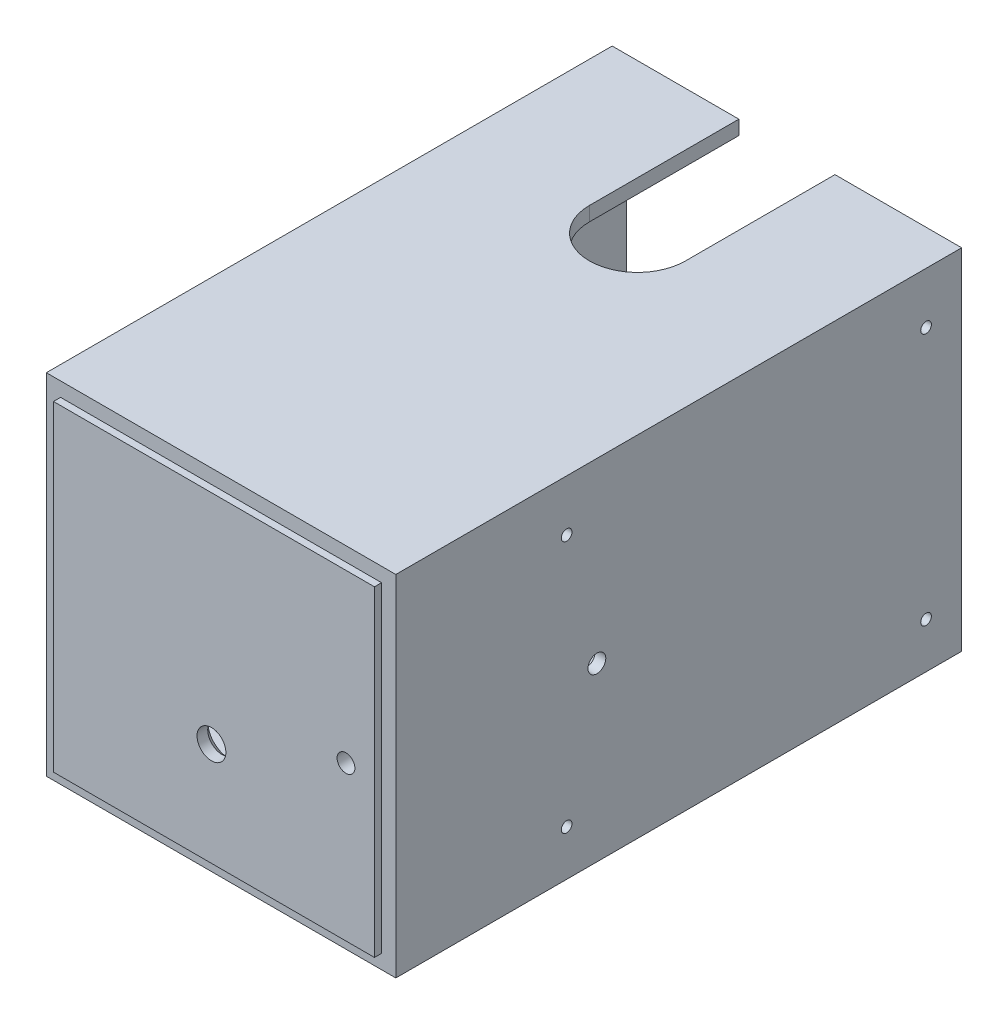
SolidWorks part; units mm, degrees
ref_plane "Alzado" through (0, 0, 0) normal (0, 0, 1) x (1, 0, 0)
ref_plane "Planta" through (0, 0, 0) normal (0, 1, 0) x (1, 0, 0)
ref_plane "Vista lateral" through (0, 0, 0) normal (1, 0, 0) x (0, 0, -1)
sketch "Croquis1" plane through (0, 0, 0) normal (0, 0, 1) x (1, 0, 0)
  line L1 (-49.1, 49.1) -> (49.1, 49.1)
  line L2 (-49.1, 49.1) -> (-49.1, -49.1)
  line L3 (-49.1, -49.1) -> (49.1, -49.1)
  line L4 (49.1, 49.1) -> (49.1, -49.1)
  point P4 (0, 49.1)
  point P6 (49.1, 0)
  dimension "D1" = 98.2
  dimension "D2" = 98.2
extrude "Saliente-Extruir1" add sketch "Croquis1" along normal blind 160.5 and the other way blind 0.5
sketch "Croquis4" plane through (0, -49.1, 0) normal (0, -1, 0) x (1, 0, 0)
  line L0 (-49.1, -0.5) -> (49.1, -0.5) construction
  line L1 (-13.5, 41.5) -> (-13.5, -0.5)
  line L2 (-13.5, -0.5) -> (13.5, -0.5)
  line L3 (13.5, -0.5) -> (13.5, 41.5)
  arc A0 (13.5, 41.5) -> (-13.5, 41.5) centre (0, 41.5) ccw
  dimension "D1" = 27
  dimension "D2" = 42
sketch "Croquis7" plane through (0, 0, -0.5) normal (0, 0, -1) x (-1, 0, 0)
  line L1 (-46.0987, 45.1) -> (45.0697, 45.1)
  line L2 (-46.0987, 45.1) -> (-46.0987, -45.1)
  line L3 (-46.0987, -45.1) -> (45.0697, -45.1)
  line L4 (45.0697, 45.1) -> (45.0697, -45.1)
  point P4 (45.0697, 0)
  dimension "D1" = 90.2
extrude "Cortar-Extruir3" cut sketch "Croquis7" against normal blind 156
extrude "puertas_laterales" cut sketch "Croquis4" against normal through all
sketch "Croquis10" plane through (0, 0, 160.5) normal (0, 0, 1) x (1, 0, 0)
  line L0 (-49.1, 49.1) -> (-49.1, -49.1) construction
  line L1 (-45.1, 45.1) -> (45.1, 45.1)
  line L2 (-45.1, 45.1) -> (-45.1, -45.1)
  line L3 (-45.1, -45.1) -> (45.1, -45.1)
  line L4 (45.1, 45.1) -> (45.1, -45.1)
  line L5 (49.1, 49.1) -> (-49.1, 49.1) construction
  line L6 (49.1, -49.1) -> (49.1, 49.1) construction
  line L7 (-49.1, -49.1) -> (49.1, -49.1) construction
  dimension "D1" = 4
  dimension "D2" = 4
  dimension "D3" = 4
  dimension "D4" = 4
extrude "parte_sup" cut sketch "Croquis10" against normal blind 2 flip side to cut
fillet "Redondeo1" radius 2 4 edges at (-45.0697, -45.1, 77.5) (-45.0697, 45.1, 77.5) (46.0987, -45.1, 77.5) (46.0987, 45.1, 77.5)
sketch "Croquis13" plane through (0, 0, 160.5) normal (0, 0, 1) x (1, 0, 0)
  line L1 (-45.1, 45.1) -> (45.1, 45.1)
  line L2 (-45.1, 45.1) -> (-45.1, -45.1)
  line L3 (-45.1, -45.1) -> (45.1, -45.1)
  line L4 (45.1, 45.1) -> (45.1, -45.1)
  line L5 (-13, -6.1) -> (13, -6.1)
  line L6 (-13, -6.1) -> (-13, -45.1)
  line L7 (-13, -45.1) -> (13, -45.1)
  line L8 (13, -6.1) -> (13, -45.1)
  line L9 (-7.5, -45.1) -> (7.2959, -45.1)
  line L10 (-7.5, -45.1) -> (-7.5, -28.18)
  line L12 (7.2959, -45.1) -> (7.2959, -30.646)
  circle A0 centre (-0.7041, -16.1) radius 4.05
  point P10 (0, -45.1)
  point P11 (0, -6.1)
  dimension "D7" = 8.1
  dimension "D8" = 44.3959
  dimension "D1" = 26
  dimension "D2" = 39
  dimension "D3" = 15
  dimension "D4" = 16.92
  dimension "D5" = 8
  dimension "D6" = 29
extrude "Cortar-Extruir7" cut sketch "Croquis13" against normal blind 6 contours A0
sketch "altura_piso_a_numeros" plane through (0, 49.1, 0) normal (0, 1, 0) x (1, 0, 0)
  line L5 (-72.9645, -59.0082) -> (89.6, -59.0082) construction
  line L6 (73.8227, -140.9384) -> (71.8227, -140.9384) construction
  dimension "D1" = 81.9302
sketch "altura_num_cam" plane through (0, 49.1, 0) normal (0, 1, 0) x (1, 0, 0)
  line L0 (48.8905, -59.0082) -> (49.1, -149.0082) construction
  line L1 (-72.9645, -59.0082) -> (89.6, -59.0082) construction
  line L2 (49.1, -158.5) -> (49.1, 0.5) construction
  dimension "D1" = 90
sketch "sim_ancho_cam" plane through (0, -49.1, 0) normal (0, -1, 0) x (1, 0, 0)
  line L0 (-49.1, 158.5) -> (49.1, 158.5) construction
  line L1 (-13, 158.5) -> (13, 158.5)
  line L4 (13, 158.5) -> (13, 142.5)
  line L5 (-13, 158.5) -> (13, 158.5)
  line L6 (-13, 158.5) -> (-13, 142.5)
  line L7 (-13, 142.5) -> (13, 142.5)
  line L8 (13, 158.5) -> (13, 142.5)
  line L9 (-13, 158.5) -> (-25, 158.5) construction
  line L10 (13, 158.5) -> (25, 158.5) construction
  line L11 (-45.1, 158.5) -> (45.1, 158.5) construction
  point P2 (0, 158.5)
  point P10 (0, 158.5)
  point P11 (0, 142.5)
  dimension "D1" = 26
  dimension "D2" = 16
  dimension "D3" = 12
  dimension "D4" = 12
sketch "Croquis29" plane through (0, 0, 160.5) normal (0, 0, 1) x (1, 0, 0)
  line L2 (-49.1, -49.1) -> (49.1, -49.1) construction
  line L3 (49.1, -49.1) -> (49.1, 49.1) construction
  circle A0 centre (37.1, -1.8) radius 2.5
  dimension "D1" = 47.3
  dimension "D3" = 5
  dimension "D2" = 12
extrude "hueco_5v_top" cut sketch "Croquis29" against normal blind 5
chamfer "Chaflán3" distance 2 angle 45 1 edges at (-4.7541, -16.1, 155.5)
sketch "Croquis33" plane through (49.1, 0, 0) normal (1, 0, 0) x (0, 0, -1)
  line L0 (0.5, 49.1) -> (-158.5, 49.1) construction
  line L1 (-107, 23.98) -> (-7, 23.98)
  line L2 (-107, 23.98) -> (-107, -24.02)
  line L3 (-107, -24.02) -> (-7, -24.02)
  line L4 (-7, 23.98) -> (-7, -24.02)
  line L6 (0.5, -49.1) -> (0.5, 49.1) construction
  dimension "D1" = 100
  dimension "D2" = 48
  dimension "D3" = 25.12
  dimension "D4" = 7.5
sketch "Croquis34" plane through (46.0987, 0, 0) normal (-1, 0, 0) x (0, 0, 1)
  line L0 (107, 23.98) -> (107, -24.02) construction
  line L1 (107, 23.98) -> (7, 23.98) construction
  line L3 (-0.5, -49.1) -> (158.5, -49.1) construction
  circle A0 centre (102, -0.8) radius 2.5
  dimension "D1" = 5
  dimension "D2" = 5
  dimension "D4" = 48.3
  dimension "D3" = 24.78
extrude "hueco5v_atras" cut sketch "Croquis34" against normal blind 4
sketch "Croquis35" plane through (49.1, 0, 0) normal (1, 0, 0) x (0, 0, -1)
  line L0 (-107, 23.98) -> (-107, 30.98)
  line L1 (-107, 23.98) -> (-100, 23.98)
  line L2 (-107, 23.98) -> (-7, 23.98) construction
  line L3 (-100, 23.98) -> (-100, 30.98)
  line L4 (-7, 23.98) -> (-14, 23.98)
  line L5 (-7, 23.98) -> (-7, 30.98)
  line L6 (-14, 23.98) -> (-14, 30.98)
  line L7 (-7, -24.02) -> (-7, -31.02)
  line L8 (-7, -24.02) -> (-14, -24.02)
  line L9 (-107, -24.02) -> (-7, -24.02) construction
  line L10 (-14, -24.02) -> (-14, -31.02)
  line L11 (-107, -24.02) -> (-100, -24.02)
  line L12 (-107, -24.02) -> (-107, -31.02)
  line L13 (-100, -24.02) -> (-100, -31.02)
  arc A0 (-100, 30.98) -> (-107, 30.98) centre (-103.5, 30.98) ccw
  circle A1 centre (-103.5, 30.98) radius 1.5
  arc A2 (-7, 30.98) -> (-14, 30.98) centre (-10.5, 30.98) ccw
  circle A3 centre (-10.5, 30.98) radius 1.5
  arc A4 (-14, -31.02) -> (-7, -31.02) centre (-10.5, -31.02) ccw
  circle A5 centre (-10.5, -31.02) radius 1.5
  arc A6 (-107, -31.02) -> (-100, -31.02) centre (-103.5, -31.02) ccw
  circle A7 centre (-103.5, -31.02) radius 1.5
  dimension "D3" = 7
  dimension "D4" = 3
  dimension "D7" = 7
  dimension "D8" = 3
  dimension "D11" = 7
  dimension "D12" = 3
  dimension "D15" = 3
  dimension "D1" = 7
  dimension "D2" = 7
  dimension "D5" = 7
  dimension "D6" = 7
  dimension "D9" = 7
  dimension "D10" = 7
  dimension "D13" = 7
  dimension "D14" = 7
sketch "Croquis37" plane through (-49.1, 0, 0) normal (-1, 0, 0) x (0, 0, 1)
  line L0 (114.4794, 20.1737) -> (60.4794, 20.1737)
  line L1 (60.4794, 20.1737) -> (60.4794, 17.3737)
  line L2 (107.4443, 28.6737) -> (57.3308, 28.6737)
  line L3 (60.4794, 17.3737) -> (116.0133, 17.3737)
  line L4 (119.0023, 8.8737) -> (45.7728, 8.8737)
  line L5 (119.6627, 4.8737) -> (45.1124, 4.8737)
  line L6 (119.6285, -3.6263) -> (45.1466, -3.6263)
  line L7 (118.9346, -7.6263) -> (81.3496, -7.6263)
  line L8 (81.3496, -7.6263) -> (81.3496, -18.9263)
  line L9 (76.153, -7.6263) -> (45.8405, -7.6263)
  line L10 (76.153, -7.6263) -> (76.153, -16.1263)
  line L11 (76.153, -16.1263) -> (58.9481, -16.1263)
  line L12 (58.9481, -16.1263) -> (58.9481, -18.9263)
  line L13 (58.9481, -18.9263) -> (81.3496, -18.9263)
  line L14 (89.371, -16.1263) -> (103.9056, -16.1263)
  line L15 (89.371, -16.1263) -> (89.371, -27.4263)
  line L16 (89.371, -27.4263) -> (57.6689, -27.4263)
  line L17 (103.9056, -16.1263) -> (103.9056, -18.9263)
  line L18 (103.9056, -18.9263) -> (93.371, -18.9263)
  line L19 (93.371, -18.9263) -> (93.371, -27.539)
  line L20 (93.371, -27.539) -> (106.977, -27.539)
  arc A0 (106.977, -27.539) -> (118.9346, -7.6263) centre (82.3876, 0.7737) ccw
  arc A1 (119.6285, -3.6263) -> (119.6627, 4.8737) centre (82.3876, 0.7737) ccw
  arc A2 (119.0023, 8.8737) -> (116.0133, 17.3737) centre (82.3876, 0.7737) ccw
  arc A3 (114.4794, 20.1737) -> (107.4443, 28.6737) centre (82.3876, 0.7737) ccw
  arc A4 (57.3308, 28.6737) -> (45.7728, 8.8737) centre (82.3876, 0.7737) ccw
  arc A5 (45.1124, 4.8737) -> (45.1466, -3.6263) centre (82.3876, 0.7737) ccw
  arc A6 (45.8405, -7.6263) -> (57.6689, -27.4263) centre (82.3876, 0.7737) ccw
  dimension "D1" = 75
  dimension "D2" = 8.5
  dimension "D3" = 8.5
  dimension "D4" = 54
  dimension "D5" = 8.5
  dimension "D6" = 4
  dimension "D7" = 8.5
  dimension "D8" = 2.8
  dimension "D9" = 4
  dimension "D10" = 2.8
  dimension "D11" = 11.3
  dimension "D12" = 8.5
  dimension "D13" = 8.5
  dimension "D14" = 2.8
  dimension "D15" = 4
extrude "logo_uis" cut sketch "Croquis37" against normal blind 1 contours L2 A4 L4 A2 L3 L1 L0 A3 | L5 A5 L6 A1 | L9 A6 L16 L15 L14 L17 L18 L19 L20 A0 L7 L8 L13 L12 L11 L10
sketch "Croquis38" plane through (49.1, 0, 0) normal (1, 0, 0) x (0, 0, -1)
  circle A0 centre (-103.5, 30.98) radius 1.5
  circle A1 centre (-10.5, 30.98) radius 1.5
  circle A2 centre (-103.5, -31.02) radius 1.5
  circle A3 centre (-10.5, -31.02) radius 1.5
  dimension "D1" = 3
  dimension "D2" = 3
  dimension "D3" = 3
  dimension "D4" = 3
sketch "Croquis39" plane through (49.1, 0, 0) normal (1, 0, 0) x (0, 0, -1)
  circle A2 centre (-110.5, -36.3) radius 1.5
  circle A3 centre (-102, -0.8) radius 2.5 construction
  circle A4 centre (-9.5, -36.3) radius 1.5
  circle A5 centre (-110.5, 34.7) radius 1.5
  circle A6 centre (-9.5, 34.7) radius 1.5
  dimension "D1" = 35.5
  dimension "D2" = 8.5
  dimension "D3" = 3
  dimension "D4" = 92.5
  dimension "D5" = 3
  dimension "D6" = 3
  dimension "D7" = 35.5
  dimension "D8" = 8.5
  dimension "D9" = 3
  dimension "D10" = 92.5
extrude "Cortar-Extruir10" cut sketch "Croquis39" against normal blind 3
